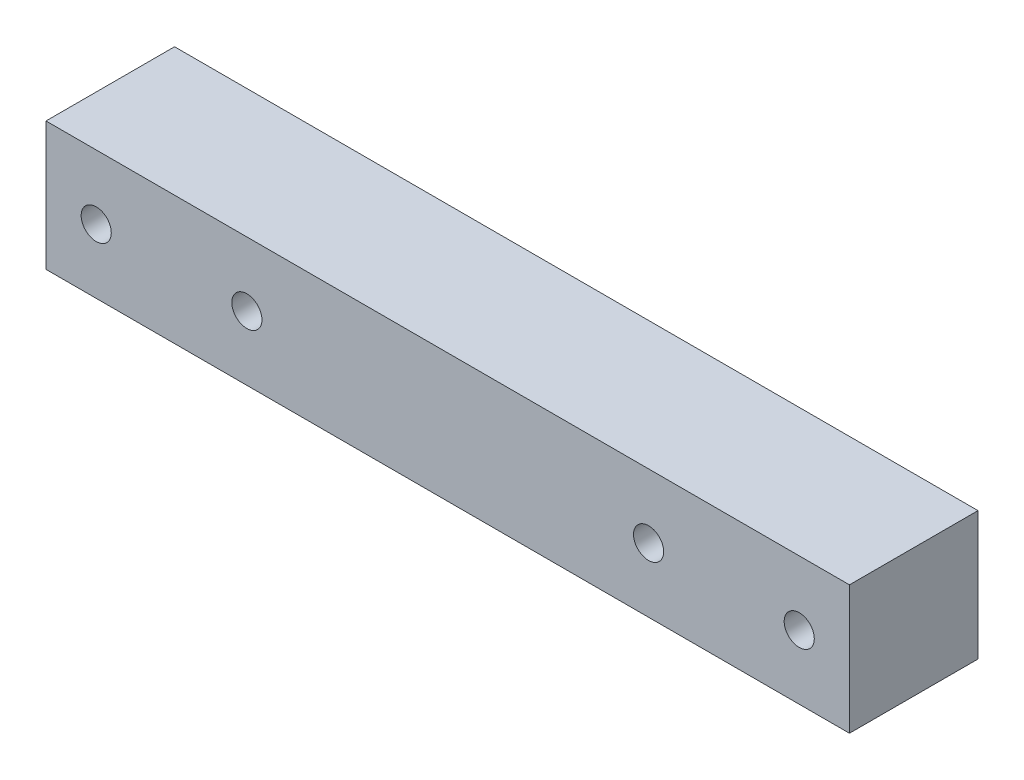
SolidWorks part; units mm, degrees
ref_plane "Plano frontal" through (0, 0, 0) normal (0, 0, 1) x (1, 0, 0)
ref_plane "Plano superior" through (0, 0, 0) normal (0, 1, 0) x (1, 0, 0)
ref_plane "Plano direito" through (0, 0, 0) normal (1, 0, 0) x (0, 0, -1)
sketch "Esboço1" plane through (0, 0, 0) normal (0, 0, 1) x (1, 0, 0)
  line L1 (0, 0) -> (80, 0)
  line L2 (0, 0) -> (0, 12.8)
  line L3 (0, 12.8) -> (80, 12.8)
  line L4 (80, 0) -> (80, 12.8)
  dimension "D1" = 12.8
  dimension "D2" = 80
extrude "Ressalto-extrusão1" add sketch "Esboço1" along normal blind 12.8
sketch "Esboço2" plane through (0, 0, 12.8) normal (0, 0, 1) x (1, 0, 0)
  line L0 (80, 6.4) -> (75, 6.4)
  line L1 (80, 0) -> (80, 12.8) construction
  line L2 (75, 6.4) -> (60, 6.4)
  line L3 (40, 12.8) -> (40, 0)
  line L4 (80, 12.8) -> (0, 12.8) construction
  line L5 (0, 0) -> (80, 0) construction
  circle A0 centre (75, 6.4) radius 1.5
  circle A1 centre (60, 6.4) radius 1.5
  circle A2 centre (5, 6.4) radius 1.5
  circle A3 centre (20, 6.4) radius 1.5
  dimension "D3" = 3
  dimension "D4" = 3
  dimension "D1" = 5
  dimension "D2" = 15
extrude "Corte-extrusão1" cut sketch "Esboço2" against normal blind 12.8
